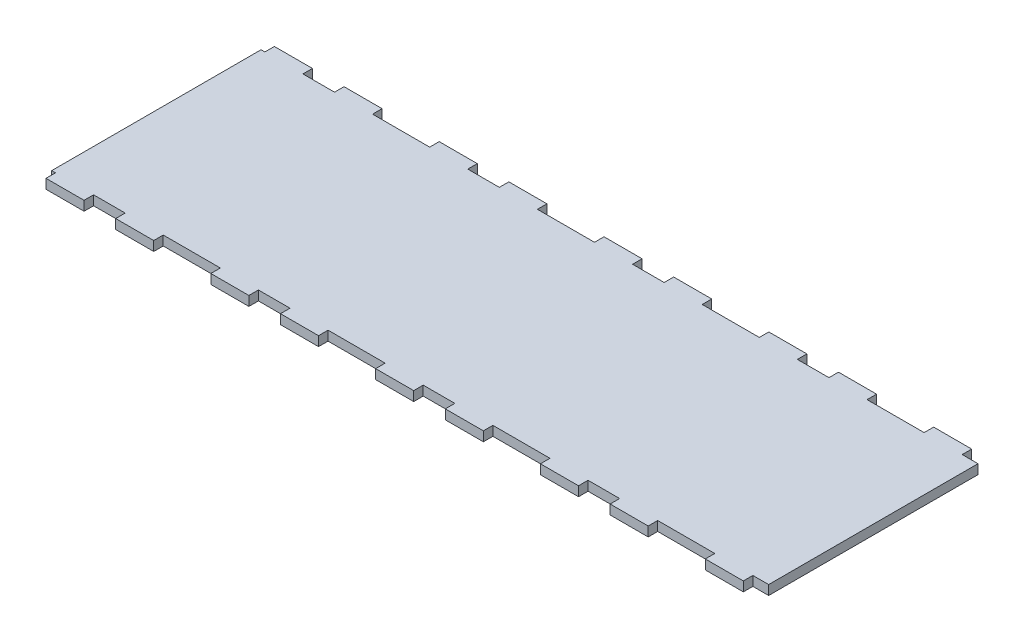
SolidWorks part; units mm, degrees
material "Cedar"
ref_plane "Front Plane" through (0, 0, 0) normal (0, 0, 1) x (1, 0, 0)
ref_plane "Top Plane" through (0, 0, 0) normal (0, 1, 0) x (1, 0, 0)
ref_plane "Right Plane" through (0, 0, 0) normal (1, 0, 0) x (0, 0, -1)
sketch "Sketch1" plane through (0, 0, 0) normal (0, 1, 0) x (1, 0, 0)
  line L1 (-258.4653, 76.2) -> (258.4653, 76.2)
  line L2 (-258.4653, 76.2) -> (-258.4653, -76.2)
  line L3 (-258.4653, -76.2) -> (258.4653, -76.2)
  line L4 (258.4653, 76.2) -> (258.4653, -76.2)
  line L5 (-258.4653, 76.2) -> (258.4653, -76.2) construction
  line L6 (-258.4653, -76.2) -> (258.4653, 76.2) construction
  point P0 (0, 0)
  dimension "D1" = 516.9306
  dimension "D2" = 152.4
extrude "Boss-Extrude1" add sketch "Sketch1" along normal blind 6.35
sketch "Sketch2" plane through (0, 6.35, 0) normal (0, 1, 0) x (1, 0, 0)
  line L0 (0, -76.2) -> (0, -69.85) construction
  line L1 (-23.2426, -69.85) -> (23.2426, -69.85) construction
  line L2 (-35.9426, -69.85) -> (-10.5426, -69.85) construction
  line L3 (-35.9426, -69.85) -> (-35.9426, -76.2) construction
  line L4 (-35.9426, -76.2) -> (-10.5426, -76.2) construction
  line L5 (-10.5426, -69.85) -> (-10.5426, -76.2)
  line L6 (-35.9426, -69.85) -> (-10.5426, -76.2) construction
  line L7 (-35.9426, -76.2) -> (-10.5426, -69.85) construction
  line L8 (-258.4653, -76.2) -> (258.4653, -76.2) construction
  line L9 (-10.5426, -69.85) -> (10.5426, -69.85)
  line L10 (10.5426, -69.85) -> (35.9426, -69.85) construction
  line L11 (10.5426, -69.85) -> (10.5426, -76.2)
  line L12 (10.5426, -76.2) -> (35.9426, -76.2) construction
  line L13 (35.9426, -69.85) -> (35.9426, -76.2) construction
  line L14 (10.5426, -69.85) -> (35.9426, -76.2) construction
  line L15 (10.5426, -76.2) -> (35.9426, -69.85) construction
  line L16 (10.5426, -76.2) -> (-10.5426, -76.2)
  line L17 (-35.9426, -76.2) -> (-35.9426, -69.85)
  line L18 (-35.9426, -69.85) -> (-54.9926, -69.85)
  line L19 (-54.9926, -69.85) -> (-54.9926, -76.2)
  line L20 (-54.9926, -76.2) -> (-35.9426, -76.2)
  line L21 (35.9426, -69.85) -> (54.9926, -69.85)
  line L22 (54.9926, -69.85) -> (54.9926, -76.2)
  line L23 (54.9926, -76.2) -> (35.9426, -76.2)
  line L24 (35.9426, -76.2) -> (35.9426, -69.85)
  point P5 (0, -69.85)
  point P6 (-23.2426, -73.025)
  point P11 (-23.2426, -69.85)
  point P17 (23.2426, -73.025)
  point P24 (23.2426, -69.85)
  dimension "D1" = 21.0852
  dimension "D2" = 25.4
  dimension "D3" = 6.35
  dimension "D4" = 54.9926
  dimension "D5" = 25.4
  dimension "D6" = 6.35
  dimension "D7" = 54.9926
extrude "Cut-Extrude1" cut sketch "Sketch2" against normal through all
pattern_linear "LPattern1" count 3 spacing 109.9852 along (1, 0, 0) count 3 spacing 109.9852 along (-1, 0, 0) of "Cut-Extrude1"
mirror "Mirror1" about plane through (0, 0, 0) normal (0, 0, 1) of "LPattern1", "Cut-Extrude1"
sketch "Sketch3" plane through (0, 6.35, 0) normal (0, 1, 0) x (1, 0, 0)
  line L0 (219.9705, 69.85) -> (219.9705, -76.2)
  line L1 (230.5131, 69.85) -> (209.4278, 69.85) construction
  line L2 (219.9705, -76.2) -> (258.4653, -76.2)
  line L3 (258.4653, -76.2) -> (258.4653, 76.2)
  line L4 (258.4653, 76.2) -> (219.9705, 76.2)
  line L5 (219.9705, 76.2) -> (219.9705, 69.85)
extrude "Cut-Extrude2" cut sketch "Sketch3" against normal through all
